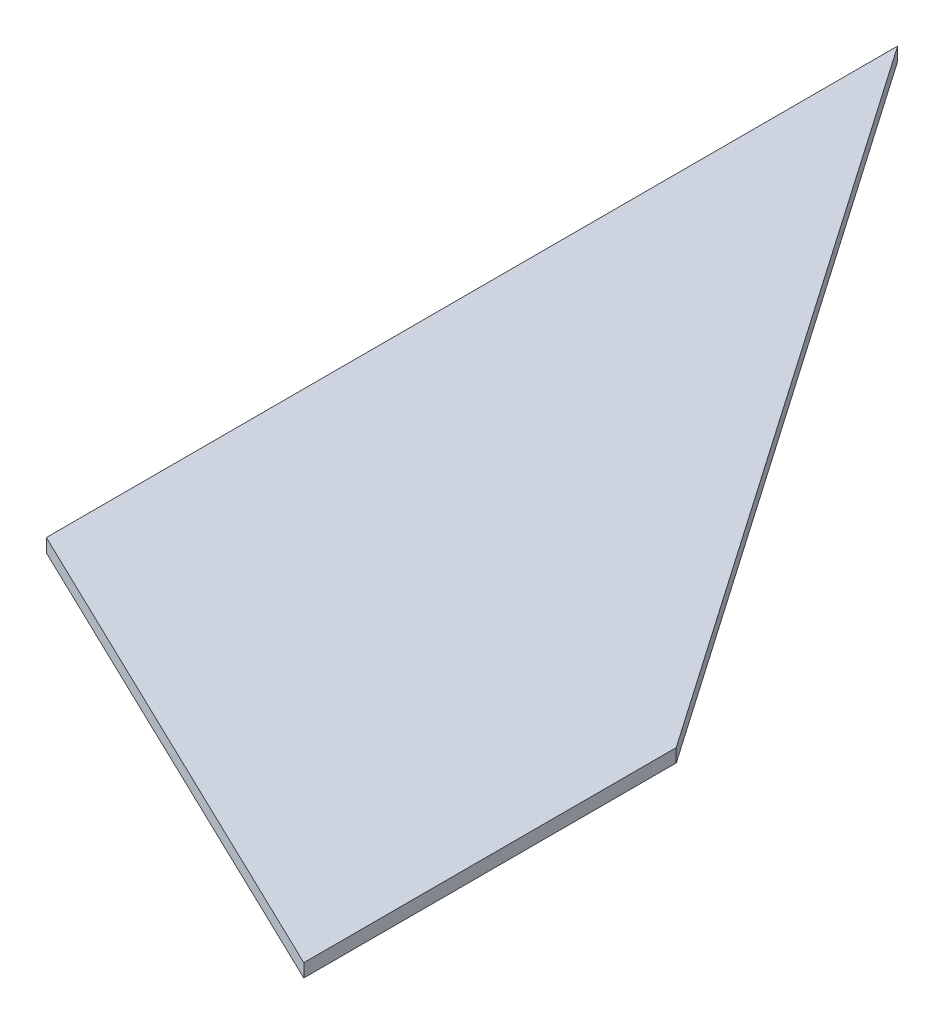
SolidWorks part; units mm, degrees
ref_plane "Front Plane" through (0, 0, 0) normal (0, 0, 1) x (1, 0, 0)
ref_plane "Top Plane" through (0, 0, 0) normal (0, 1, 0) x (1, 0, 0)
ref_plane "Right Plane" through (0, 0, 0) normal (1, 0, 0) x (0, 0, -1)
sketch "Sketch1" plane through (0, 0, 0) normal (0, 1, 0) x (1, 0, 0)
  line L0 (0, 0) -> (0, 124.3147) construction
  line L1 (0, 0) -> (0, 203.2)
  line L2 (0, 203.2) -> (118.5992, 31.75)
  line L3 (118.5992, 31.75) -> (118.5992, -57.15)
  line L4 (118.5992, -57.15) -> (0, 0)
  dimension "D1" = 203.2
  dimension "D2" = 171.45
  dimension "D3" = 88.9
extrude "Boss-Extrude1" add sketch "Sketch1" along normal blind 3.175
sketch "Sketch2" plane through (118.5992, 0, 0) normal (1, 0, 0) x (0, 0, -1)
  line L0 (31.75, 1.5875) -> (-12.7, 3.175)
  line L1 (31.75, 3.175) -> (31.75, 0) construction
  line L2 (-57.15, 3.175) -> (31.75, 3.175) construction
  line L3 (-12.7, 3.175) -> (-57.15, 1.5875)
  line L4 (-57.15, 3.175) -> (-57.15, 0) construction
  line L5 (-57.15, 1.5875) -> (-12.7, 0)
  line L6 (-57.15, 0) -> (31.75, 0) construction
  line L7 (-12.7, 0) -> (31.75, 1.5875)
sketch "Sketch3" plane through (0, 0, 0) normal (-1, 0, 0) x (0, 0, 1)
  line L0 (-203.2, 1.5875) -> (-101.6, 3.175)
  line L1 (-203.2, 3.175) -> (-203.2, 0) construction
  line L2 (-203.2, 3.175) -> (0, 3.175) construction
  line L3 (-101.6, 3.175) -> (0, 1.5875)
  line L4 (0, 3.175) -> (0, 0) construction
  line L5 (0, 1.5875) -> (-101.6, 0)
  line L6 (-203.2, 0) -> (0, 0) construction
  line L7 (-101.6, 0) -> (-203.2, 1.5875)
sketch "Sketch4" plane through (95.0702, 0, -65.7641) normal (0.8224, 0, -0.5689) x (-0.5689, 0, -0.8224)
  line L0 (-41.359, 1.5875) -> (167.1137, 1.5875)
sketch "Sketch5" plane through (0, 3.175, 0) normal (0, 1, 0) x (1, 0, 0)
  line L0 (0, 101.6) -> (118.5992, -12.7)
  line L1 (0, 101.6) -> (0, 203.2) construction
  line L2 (118.5992, -12.7) -> (118.5992, 31.75) construction
